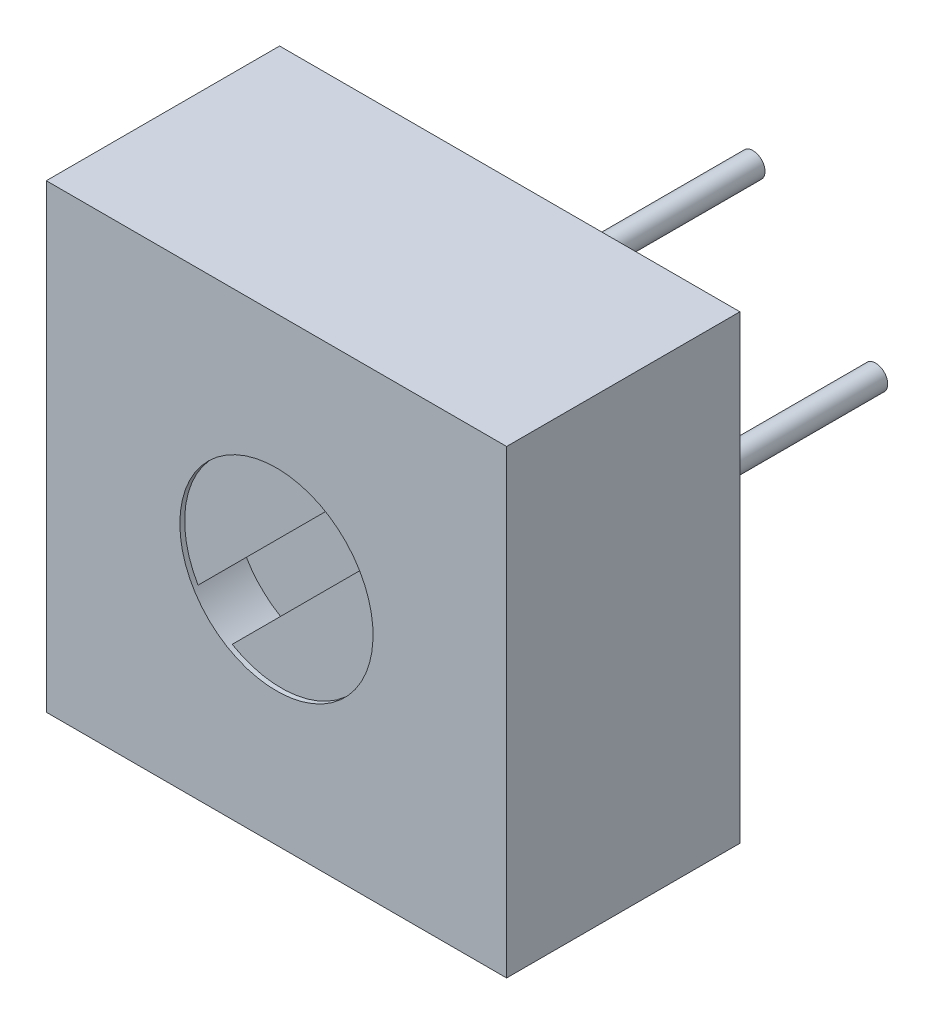
SolidWorks part; units mm, degrees
ref_plane "Front Plane" through (0, 0, 0) normal (0, 0, 1) x (1, 0, 0)
ref_plane "Top Plane" through (0, 0, 0) normal (0, 1, 0) x (1, 0, 0)
ref_plane "Right Plane" through (0, 0, 0) normal (1, 0, 0) x (0, 0, -1)
sketch "Sketch1" plane through (0, 0, 0) normal (0, 0, -1) x (1, 0, 0)
  line L0 (0, 0) -> (9.53, 0)
  line L1 (0, 0) -> (0, 9.53)
  line L2 (9.53, 9.53) -> (0, 9.53)
  line L3 (9.53, 9.53) -> (9.53, 0)
  dimension "D1" = 9.53
extrude "Basic Shape" add sketch "Sketch1" along normal blind 4.83
sketch "Sketch2" plane through (0, 0, -4.83) normal (0, 0, 1) x (1, 0, 0)
  line L0 (0, 0) -> (0, -9.53) construction
  line L1 (9.53, -9.53) -> (9.53, 0) construction
  circle A0 centre (4.8, -7.305) radius 0.25
  circle A1 centre (4.8, -2.225) radius 0.25
  circle A2 centre (7.34, -4.765) radius 0.25
  point P8 (9.53, -4.765)
  dimension "D5" = 0.5
  dimension "D1" = 4.8
  dimension "D2" = 2.54
  dimension "D3" = 2.54
  dimension "D4" = 2.54
extrude "Pins" add sketch "Sketch2" against normal blind 5
sketch "Sketch3" plane through (0, 0, 0) normal (0, 0, -1) x (-1, 0, 0)
  line L0 (-9.53, -9.53) -> (-9.53, 0) construction
  line L1 (0, 0) -> (-9.53, 0) construction
  circle A0 centre (-4.765, -4.765) radius 2
  point P2 (-9.53, -4.765)
  point P3 (-4.765, 0)
  dimension "D1" = 4
extrude "Adjuster" cut sketch "Sketch3" along normal blind 0.1
sketch "Sketch4" plane through (0, 0, -0.1) normal (0, 0, 1) x (-1, 0, 0)
  line L0 (-6.4879, 3.7492) -> (-3.7492, 6.4879)
  line L1 (-5.7808, 3.0421) -> (-3.0421, 5.7808)
  line L2 (-5.1186, 5.1186) -> (-4.4114, 4.4114) construction
  line L3 (-9.53, 9.53) -> (-9.53, 0) construction
  circle A0 centre (-4.765, 4.765) radius 2 construction
  arc A1 (-6.4879, 3.7492) -> (-5.7808, 3.0421) centre (-4.765, 4.765) ccw
  arc A2 (-3.0421, 5.7808) -> (-3.7492, 6.4879) centre (-4.765, 4.765) ccw
  point P6 (-4.765, 4.765)
  dimension "D2" = 45
  dimension "D1" = 1
extrude "Adjuster Slot" cut sketch "Sketch4" against normal blind 1
ref_plane "Board Plane" through (0, 0, -6) normal (0, 0, 1) x (1, 0, 0)
sketch "Component_Outline" plane through (0, 0, -6) normal (0, 0, 1) x (1, 0, 0)
  line L1 (9.53, 0) -> (0, 0)
  line L2 (9.53, 0) -> (9.53, -9.53)
  line L3 (9.53, -9.53) -> (0, -9.53)
  line L4 (0, 0) -> (0, -9.53)
